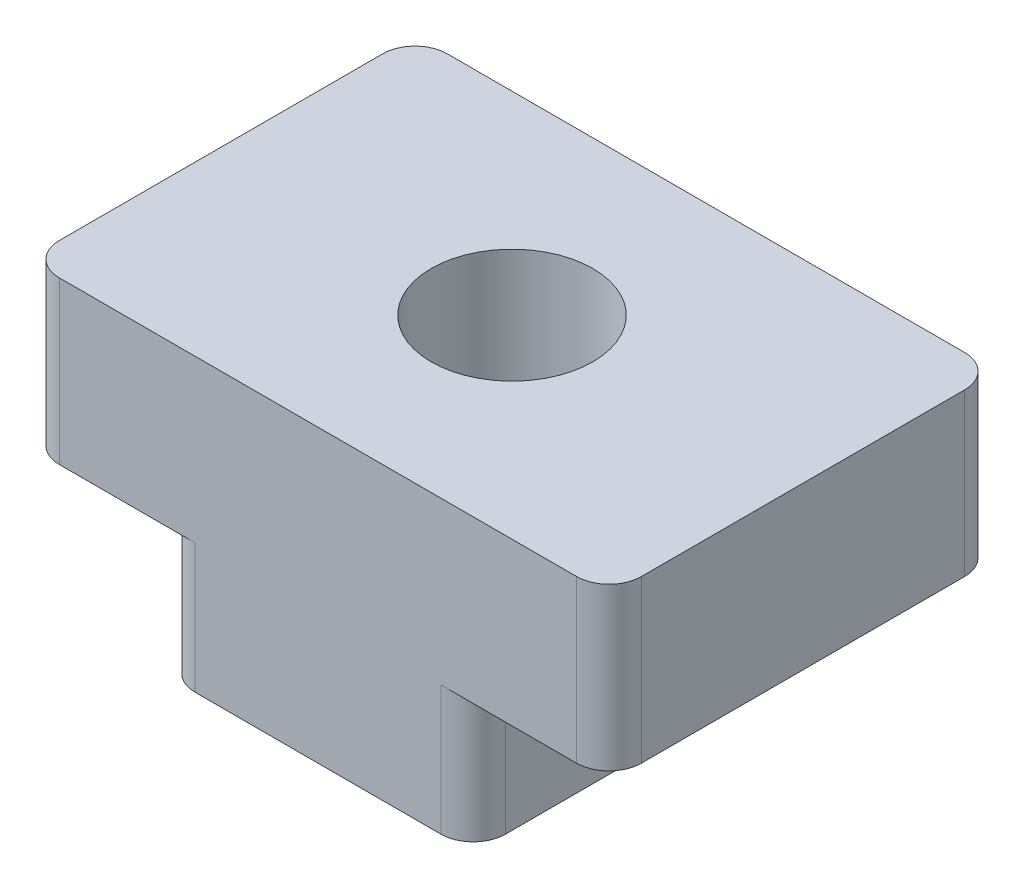
SolidWorks part; units mm, degrees
ref_plane "Plan de face" through (0, 0, 0) normal (0, 0, 1) x (1, 0, 0)
ref_plane "Plan de dessus" through (0, 0, 0) normal (0, 1, 0) x (1, 0, 0)
ref_plane "Plan de droite" through (0, 0, 0) normal (1, 0, 0) x (0, 0, -1)
sketch "Esquisse1" plane through (0, 0, 0) normal (0, 0, 1) x (1, 0, 0)
  line L0 (-4.5, 0) -> (-2.4, 0)
  line L1 (-2.4, -2) -> (2.4, -2)
  line L2 (-4.5, 0) -> (-4.5, 2.5)
  line L3 (-4.5, 2.5) -> (4.5, 2.5)
  line L4 (4.5, 0) -> (4.5, 2.5)
  line L5 (-4.5, 0) -> (4.5, 0) construction
  line L7 (-2.4, 0) -> (-2.4, -2)
  line L8 (4.5, 0) -> (2.4, 0)
  line L9 (2.4, 0) -> (2.4, -2)
  point P0 (0, 0)
  dimension "D1" = 9
  dimension "D2" = 4.8
  dimension "D3" = 2.5
  dimension "D4" = 2
extrude "Boss.-Extru.1" add sketch "Esquisse1" along normal mid plane 6
sketch "Esquisse2" plane through (0, 2.5, 0) normal (0, 1, 0) x (1, 0, 0)
  circle A0 centre (0, 0) radius 1.25
  dimension "D1" = 2.5
extrude "Enlèv. mat.-Extru.1" cut sketch "Esquisse2" against normal through all
fillet "Congé1" radius 0.5 8 edges at (-4.5, 1.25, -3) (-2.4, -1, -3) (2.4, -1, -3) (4.5, 1.25, -3) (2.4, -1, 3) (-2.4, -1, 3) (-4.5, 1.25, 3) (4.5, 1.25, 3)
sketch "Esquisse3" plane through (0, 0, 0) normal (0, -1, 0) x (1, 0, 0)
  line L0 (2.4, 2.5) -> (2.4, -2.5) construction
  line L1 (-2.4, -1.25) -> (2.4, -1.25)
  line L2 (-2.4, -1.25) -> (-2.4, 1.25)
  line L3 (-2.4, 1.25) -> (2.4, 1.25)
  line L4 (2.4, -1.25) -> (2.4, 1.25)
  line L5 (-2.4, -1.25) -> (2.4, 1.25) construction
  line L6 (-2.4, 1.25) -> (2.4, -1.25) construction
  circle A0 centre (0, 0) radius 1.25 construction
  point P0 (0, 0)
